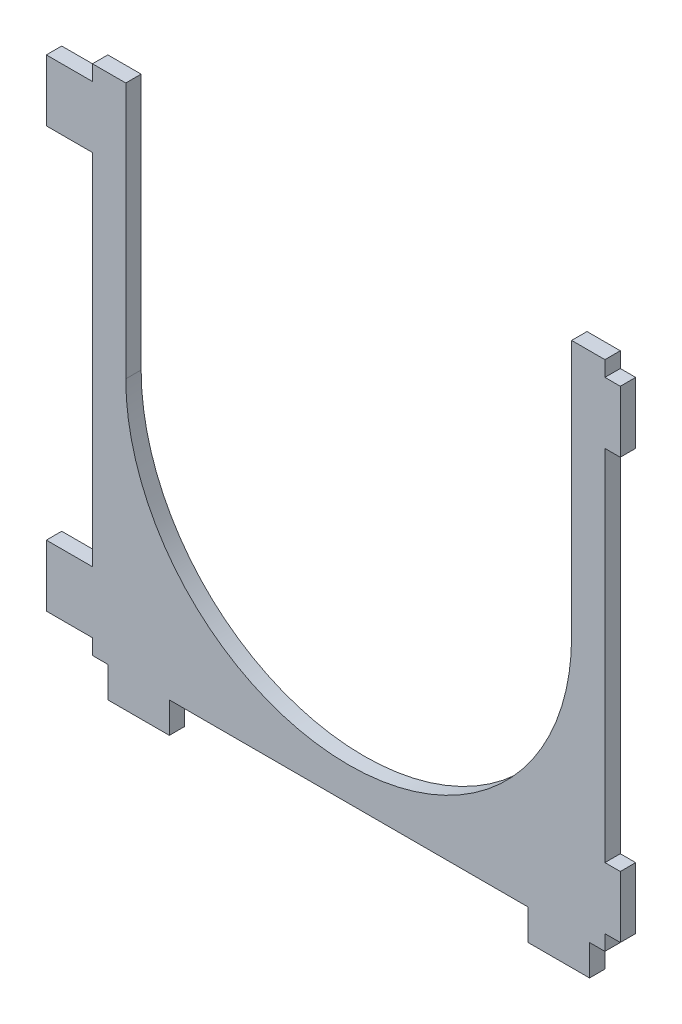
SolidWorks part; units mm, degrees
ref_plane "Alzado" through (0, 0, 0) normal (0, 0, 1) x (1, 0, 0)
ref_plane "Planta" through (0, 0, 0) normal (0, 1, 0) x (1, 0, 0)
ref_plane "Vista lateral" through (0, 0, 0) normal (1, 0, 0) x (0, 0, -1)
sketch "Croquis1" plane through (0, 0, 0) normal (0, 0, 1) x (1, 0, 0)
  line L1 (-50, -50) -> (50, -50)
  line L2 (-50, -50) -> (-50, 50)
  line L3 (-50, 50) -> (50, 50)
  line L4 (50, -50) -> (50, 50)
  line L5 (-50, -50) -> (50, 50) construction
  line L6 (-50, 50) -> (50, -50) construction
  circle A0 centre (0, 0) radius 43.5
  dimension "D1" = 87
  dimension "D2" = 100
  dimension "D3" = 100
extrude "Saliente-Extruir1" add sketch "Croquis1" along normal blind 3
sketch "Croquis2" plane through (0, 0, 3) normal (0, 0, 1) x (1, 0, 0)
  line L0 (0, 50) -> (0, -50) construction
  line L1 (-47, -50) -> (-35, -50)
  line L2 (-47, -50) -> (-47, -56)
  line L3 (-47, -56) -> (-35, -56)
  line L4 (-35, -50) -> (-35, -56)
  line L5 (50, 50) -> (-50, 50) construction
  line L6 (-50, -50) -> (50, -50) construction
  line L7 (47, -56) -> (35, -56)
  line L8 (35, -50) -> (35, -56)
  line L9 (47, -50) -> (35, -50)
  line L10 (47, -50) -> (47, -56)
  line L11 (-50, 50) -> (-50, -50) construction
  line L12 (-50, -47) -> (-59, -47)
  line L13 (-50, -47) -> (-50, -35)
  line L14 (-50, -35) -> (-59, -35)
  line L15 (-59, -47) -> (-59, -35)
  line L16 (50, -50) -> (50, 50) construction
  line L17 (50, -47) -> (53, -47)
  line L18 (50, -47) -> (50, -35)
  line L19 (50, -35) -> (53, -35)
  line L20 (53, -47) -> (53, -35)
  line L21 (-50, 0) -> (50, 0) construction
  line L22 (50, 35) -> (53, 35)
  line L23 (53, 47) -> (53, 35)
  line L24 (50, 47) -> (53, 47)
  line L25 (50, 47) -> (50, 35)
  line L26 (-50, 35) -> (-59, 35)
  line L27 (-59, 47) -> (-59, 35)
  line L28 (-50, 47) -> (-59, 47)
  line L29 (-50, 47) -> (-50, 35)
  dimension "D1" = 6
  dimension "D2" = 12
  dimension "D3" = 3
  dimension "D4" = 9
  dimension "D5" = 12
  dimension "D6" = 3
  dimension "D7" = 3
  dimension "D8" = 12
  dimension "D9" = 3
extrude "Saliente-Extruir2" add sketch "Croquis2" against normal blind 3
sketch "Croquis3" plane through (0, 0, 3) normal (0, 0, 1) x (1, 0, 0)
  line L0 (50, 50) -> (-50, 50) construction
  line L1 (-43.5, 0) -> (43.5, 0)
  line L2 (-43.5, 0) -> (-43.5, 50)
  line L3 (-43.5, 50) -> (43.5, 50)
  line L4 (43.5, 0) -> (43.5, 50)
  circle A0 centre (0, 0) radius 43.5 construction
  point P8 (43.5, 0)
  point P9 (43.5, 50)
  point P10 (43.5, 0)
  dimension "D1" = 87
extrude "Cortar-Extruir1" cut sketch "Croquis3" against normal blind 10
